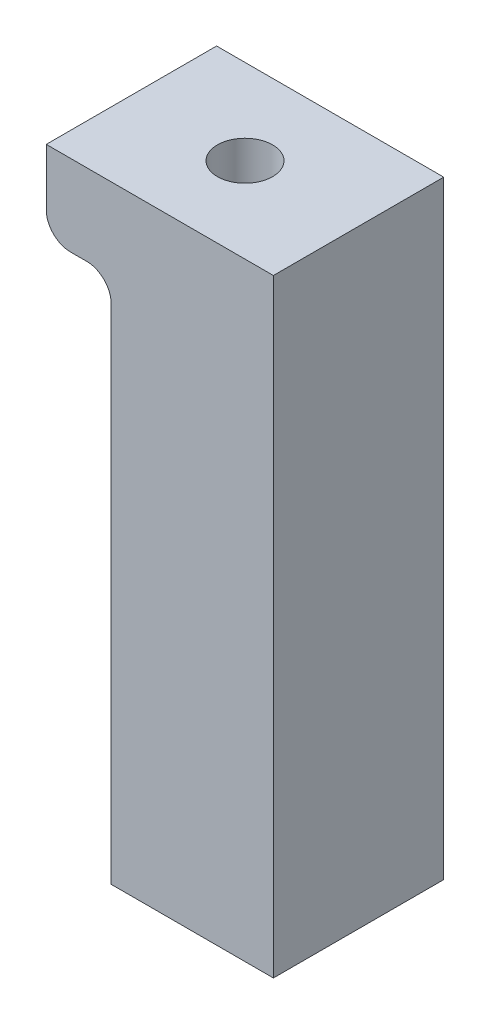
SolidWorks part; units mm, degrees
material "6061 合金"
ref_plane "前视基准面" through (0, 0, 0) normal (0, 0, 1) x (1, 0, 0)
ref_plane "上视基准面" through (0, 0, 0) normal (0, 1, 0) x (1, 0, 0)
ref_plane "右视基准面" through (0, 0, 0) normal (1, 0, 0) x (0, 0, -1)
sketch "草图1" plane through (0, 0, 0) normal (0, 1, 0) x (1, 0, 0)
  line L1 (-14, 10.5) -> (14, 10.5)
  line L2 (-14, 10.5) -> (-14, -10.5)
  line L3 (-14, -10.5) -> (14, -10.5)
  line L4 (14, 10.5) -> (14, -10.5)
  line L5 (-14, 10.5) -> (14, -10.5) construction
  line L6 (-14, -10.5) -> (14, 10.5) construction
  circle A0 centre (0, 0) radius 14 construction
  dimension "D1" = 28
  dimension "D2" = 28
  dimension "D3" = 21
extrude "凸台-拉伸1" add sketch "草图1" along normal up to surface (75 mm away)
sketch "草图3" plane through (0, 75, 0) normal (0, 1, 0) x (1, 0, 0)
  line L0 (-14, 0) -> (14, 0) construction
  line L1 (0, 0) -> (0, 10.5) construction
  line L2 (14, 10.5) -> (-14, 10.5) construction
  line L3 (14, -10.5) -> (14, 10.5) construction
  line L4 (-14, 10.5) -> (-14, -10.5) construction
  point P12 (0, 10.5)
  point P16 (14, 0)
  point P19 (-14, 0)
sketch "草图4" plane through (0, 0, 0) normal (0, -1, 0) x (-1, 0, 0)
  line L0 (14, 0) -> (-14, 0) construction
  line L1 (0, 0) -> (0, 10.5) construction
hole_wizard "M8 螺纹孔1" positions "3D草图2" profile "草图5" tap size "M8" standard "GB"
sketch3d "3D草图2"
  point P5 (0, 0, 0)
  point P7 (0, 75, 0)
  point P10 (0, 0, 0)
  point P11 (0, 0, 0)
  point P13 (0, 0, 0)
sketch "草图5" plane through (0, 75, 0) normal (1, 0, 0) x (0, 0, 1)
  line L0 (0, 0) -> (0, 21.7929)
  line L1 (0, 21.7929) -> (3.4, 19.75)
  line L2 (3.4, 19.75) -> (3.4, 0)
  line L5 (3.4, 0) -> (0, 0)
  line L10 (0, 21.7929) -> (-3.4, 19.75) construction
  line L11 (0, -6.35) -> (0, 107.95) construction
  dimension "螺纹孔钻头直径" = 6.8
  dimension "螺纹孔钻头深度" = 19.75
  dimension "导头角度" = 118
cosmetic thread "孔螺蚊线1" parameters "D1"=16, "D2"=8
sketch "草图6" plane through (0, 0, 10.5) normal (0, 0, 1) x (1, 0, 0)
  line L1 (-14, 0) -> (-6, 0)
  line L2 (-14, 0) -> (-14, 65)
  line L3 (-14, 65) -> (-6, 65)
  line L4 (-6, 0) -> (-6, 65)
  dimension "D1" = 8
  dimension "D2" = 65
extrude "切除-拉伸1" cut sketch "草图6" against normal through all
ref_plane "基准面1" through (0, 0, 0) normal (1, 0, 0) x (0, 0, -1)
mirror "镜向1" [suppressed] about plane through (0, 0, 0) normal (1, 0, 0)
fillet "圆角1" [suppressed] radius 2
fillet "圆角3" radius 3 2 edges at (-6, 65, 0) (-14, 65, 0)
hole_wizard "M6 螺纹孔1" positions "3D草图4" profile "草图8" tap size "M6" standard "GB"
sketch3d "3D草图4"
  point P0 (0, 0, 0)
sketch "草图8" plane through (0, 0, 0) normal (1, 0, 0) x (0, 0, -1)
  line L0 (0, 0) -> (0, 21.2522)
  line L1 (0, 21.2522) -> (2.5, 19.75)
  line L2 (2.5, 19.75) -> (2.5, 0)
  line L5 (2.5, 0) -> (0, 0)
  line L10 (0, 21.2522) -> (-2.5, 19.75) construction
  line L11 (0, -6.35) -> (0, 107.95) construction
  dimension "螺纹孔钻头直径" = 5
  dimension "螺纹孔钻头深度" = 19.75
  dimension "导头角度" = 118
cosmetic thread "孔螺蚊线2" parameters "D1"=12, "D2"=6
